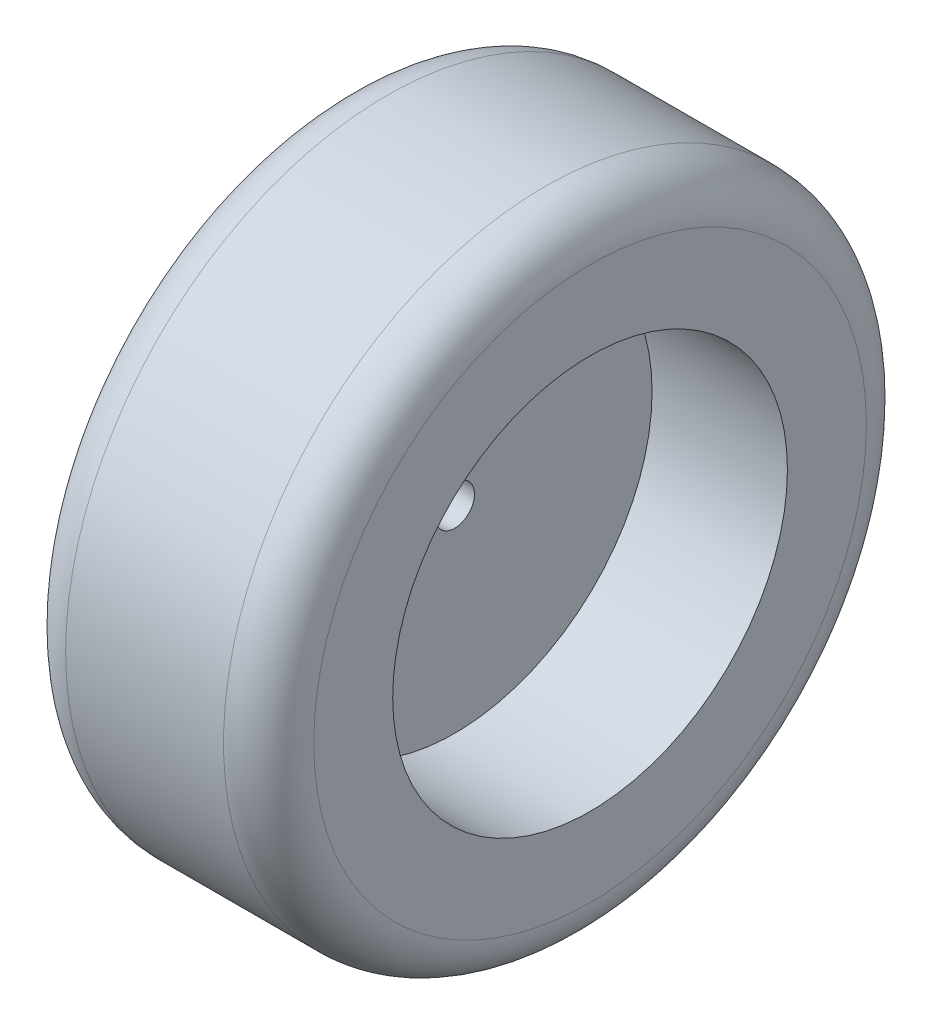
SolidWorks part; units mm, degrees
ref_plane "Front Plane" through (0, 0, 0) normal (0, 0, 1) x (1, 0, 0)
ref_plane "Top Plane" through (0, 0, 0) normal (0, 1, 0) x (1, 0, 0)
ref_plane "Right Plane" through (0, 0, 0) normal (1, 0, 0) x (0, 0, -1)
sketch "Sketch1" plane through (0, 0, 0) normal (0, 1, 0) x (1, 0, 0)
  line L0 (11, 0) -> (-11, 0)
  line L2 (-11, 0) -> (-11, 28.5)
  line L3 (-11, 28.5) -> (11, 28.5)
  line L4 (11, 0) -> (11, 28.5)
  line L5 (0, 0) -> (11, 28.5) construction
  line L6 (-11, 28.5) -> (0, 0) construction
  point P0 (0, 0)
  point P2 (0, 0)
  point P4 (0, 0)
  point P9 (10.9354, 0)
  dimension "D1" = 28.5
  dimension "D2" = 22
revolve "Revolve1" add sketch "Sketch1" angle 360 about L0
fillet "Fillet1" radius 4 2 edges at (11, 0, -28.5) (-11, 0, -28.5)
sketch "Sketch2" plane through (11, 0, 0) normal (1, 0, 0) x (0, 0, -1)
  circle A0 centre (0, 0) radius 17.5
  dimension "D1" = 35
extrude "Cut-Extrude1" cut sketch "Sketch2" against normal blind 12
sketch "Sketch3" plane through (-11, 0, 0) normal (-1, 0, 0) x (0, 0, 1)
  circle A0 centre (0, 0) radius 17.5
  circle A1 centre (0, 0) radius 17.5 construction
extrude "Cut-Extrude2" cut sketch "Sketch3" against normal offset from surface (8 mm away) 2 up to face at (-1, 0, -17.5)
sketch "Sketch4" plane through (-1, 0, 0) normal (1, 0, 0) x (0, 0, -1)
  circle A0 centre (0, 0) radius 1.75
  dimension "D1" = 3.5
extrude "Cut-Extrude3" cut sketch "Sketch4" against normal through all
